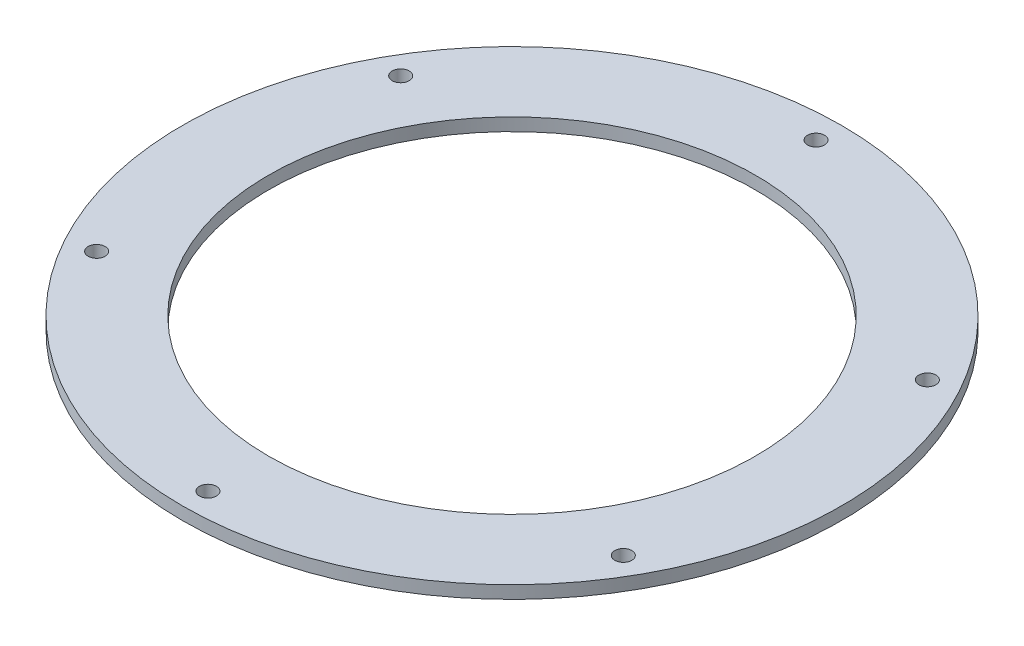
SolidWorks part; units mm, degrees
ref_plane "Front Plane" through (0, 0, 0) normal (0, 0, 1) x (1, 0, 0)
ref_plane "Top Plane" through (0, 0, 0) normal (0, 1, 0) x (1, 0, 0)
ref_plane "Right Plane" through (0, 0, 0) normal (1, 0, 0) x (0, 0, -1)
sketch "Sketch1" plane through (0, 0, 0) normal (0, 1, 0) x (1, 0, 0)
  circle A0 centre (0, 0) radius 67.4975
  circle A1 centre (0, 0) radius 63.945
  circle A2 centre (0, 0) radius 59.7406
  circle A3 centre (0, 0) radius 77.4975
  dimension "D1" = 127.89
  dimension "D2" = 134.995
  dimension "D3" = 7.7569
  dimension "D4" = 10
sketch "Sketch2" plane through (0, 0, 0) normal (0, 1, 0) x (1, 0, 0)
  line L0 (-1.65, 0) -> (1.65, 0) construction
  circle A0 centre (0, 0) radius 77.4975
  circle A1 centre (0, 0) radius 57.2406
  circle A2 centre (0, 0) radius 77.4975 construction
  circle A3 centre (0, 0) radius 59.7406 construction
  circle A4 centre (0, 0) radius 71.5 construction
  circle A5 centre (0, 71.5) radius 2
  circle A6 centre (61.9208, 35.75) radius 2
  circle A7 centre (61.9208, -35.75) radius 2
  circle A8 centre (0, -71.5) radius 2
  circle A9 centre (-61.9208, -35.75) radius 2
  circle A10 centre (-61.9208, 35.75) radius 2
  point P11 (-59.7406, 0)
  point P12 (-57.2406, 0)
  point P28 (0, 0)
  dimension "D1" = 2.5
  dimension "D2" = 143
  dimension "D3" = 4
  dimension "D4" = 6
extrude "Boss-Extrude1" add sketch "Sketch2" along normal blind 3
equation "\"m\" = 3.5'Module"
equation "\"N\"= 36'Number of teeth"
equation "\"dP\" = \"m\" * \"N\" * \"sF\"'Pitch diameter"
equation "\"D1@Sketch1\"= \"dP\""
equation "\"dA\" = ( \"N\" + 2 ) * \"m\" * \"sF\"'Addendum diameter"
equation "\"rD\" = \"m\" * IIF ( \"m\" = > 1.25 , 2.25 , 2.4 ) * ( 2 - \"sF\" )'Root diameter depth"
equation "\"t\"= 20'Gear thickness"
equation "\"D2@Sketch1\"=\"dA\""
equation "\"D3@Sketch1\"=\"rD\""
equation "\"pA\"= 20'Pressure angle"
equation "\"sA\"= 180 / \"N\"'Spacing angle"
equation "\"hA\"= 10'Helix angle"
equation "\"rT\"= 10'Ring thickness"
equation "\"D4@Sketch1\"=\"rT\""
equation "\"sF\"= 1.015'Scale factor"
